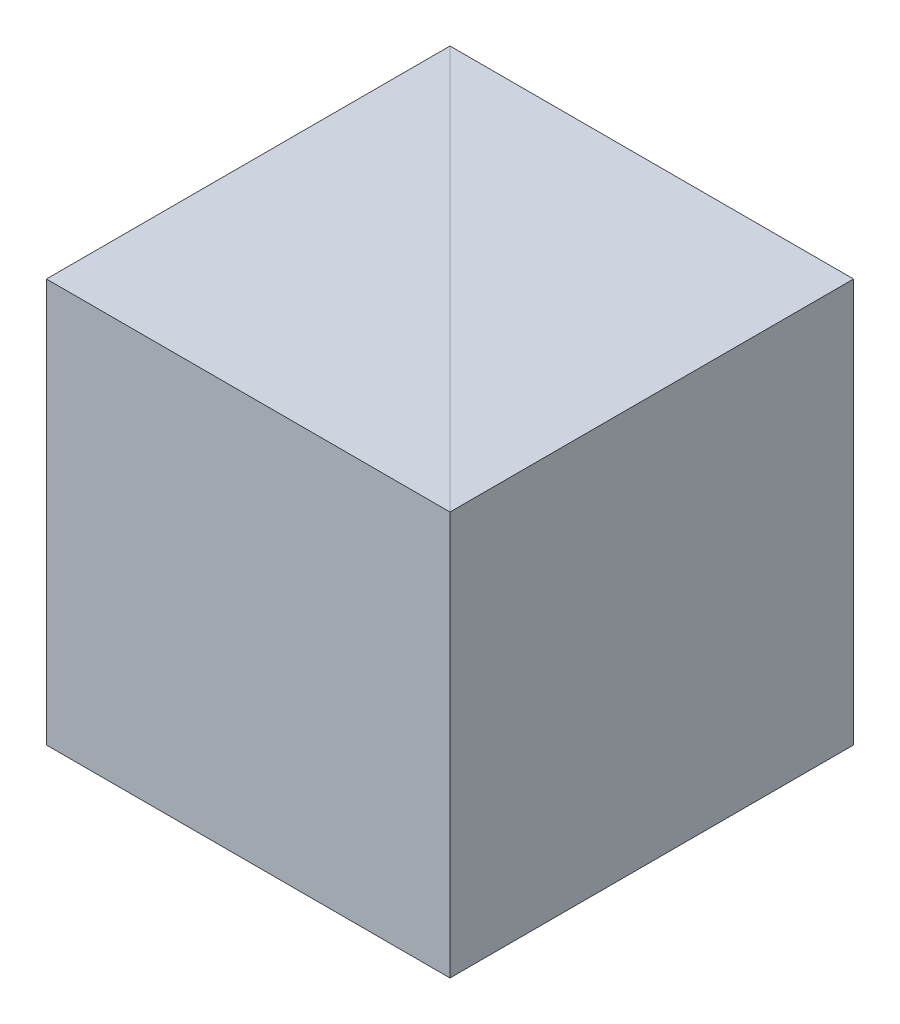
SolidWorks part; units mm, degrees
ref_plane "前视基准面" through (0, 0, 0) normal (0, 0, 1) x (1, 0, 0)
ref_plane "上视基准面" through (0, 0, 0) normal (0, 1, 0) x (1, 0, 0)
ref_plane "右视基准面" through (0, 0, 0) normal (1, 0, 0) x (0, 0, -1)
sketch "草图1" plane through (0, 0, 0) normal (0, 1, 0) x (1, 0, 0)
  line L0 (0, 0) -> (0, 15)
  line L1 (0, 15) -> (-15, 15)
  line L2 (-15, 15) -> (0, 0)
  dimension "D1" = 15
  dimension "D2" = 15
extrude "凸台-拉伸1" add sketch "草图1" along normal blind 15
sketch "草图2" plane through (0, 0, 0) normal (0, -1, 0) x (1, 0, 0)
  line L0 (-15, -15) -> (-15, 0)
  line L1 (-15, 0) -> (0, 0)
  line L2 (0, 0) -> (-15, -15)
extrude "凸台-拉伸2" add sketch "草图2" against normal blind 15 separate body
